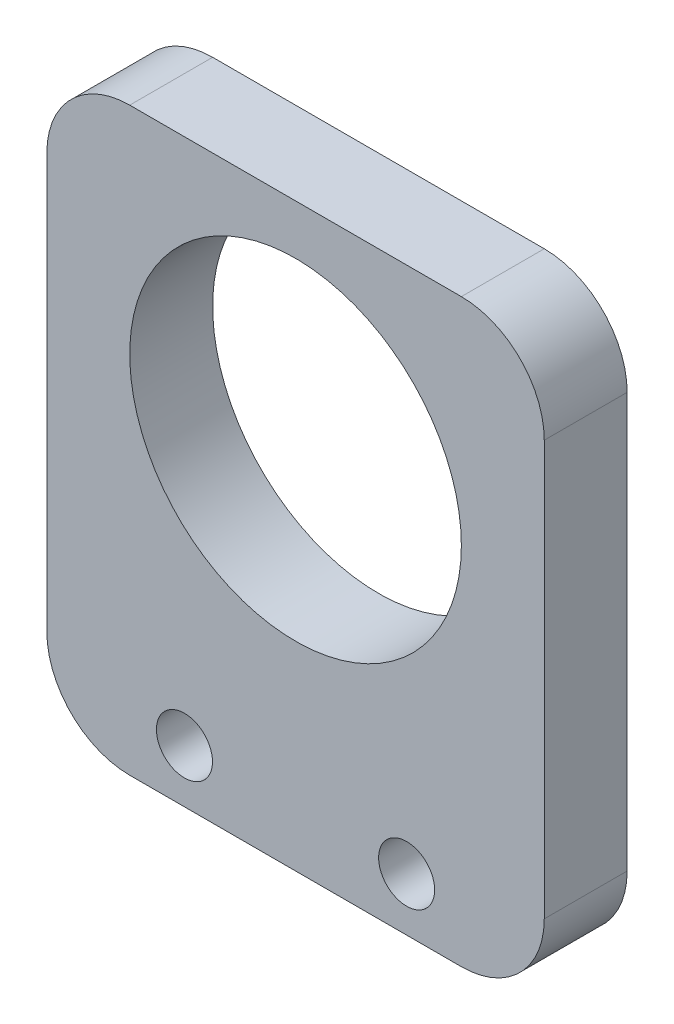
SolidWorks part; units mm, degrees
ref_plane "Front Plane" through (0, 0, 0) normal (0, 0, 1) x (1, 0, 0)
ref_plane "Top Plane" through (0, 0, 0) normal (0, 1, 0) x (1, 0, 0)
ref_plane "Right Plane" through (0, 0, 0) normal (1, 0, 0) x (0, 0, -1)
sketch "Sketch1" plane through (0, 0, 0) normal (0, 0, 1) x (1, 0, 0)
  line L0 (-19.05, 0) -> (19.05, 0)
  line L1 (19.05, 0) -> (19.05, 44.45)
  line L2 (19.05, 44.45) -> (-19.05, 44.45)
  line L3 (0, 0) -> (0, 62.7572) construction
  line L4 (-19.05, 0) -> (-19.05, 44.45)
  circle A0 centre (0, 27.94) radius 12.7
  circle A1 centre (8.509, 4.064) radius 2.1463
  circle A2 centre (-8.509, 4.064) radius 2.1463
  point P7 (0, 44.45)
  dimension "D1" = 19.05
  dimension "D2" = 44.45
extrude "Boss-Extrude1" add sketch "Sketch1" along normal blind 6.35
fillet "Fillet1" radius 6.35 4 edges at (-19.05, 44.45, 3.175) (-19.05, 0, 3.175) (19.05, 0, 3.175) (19.05, 44.45, 3.175)
